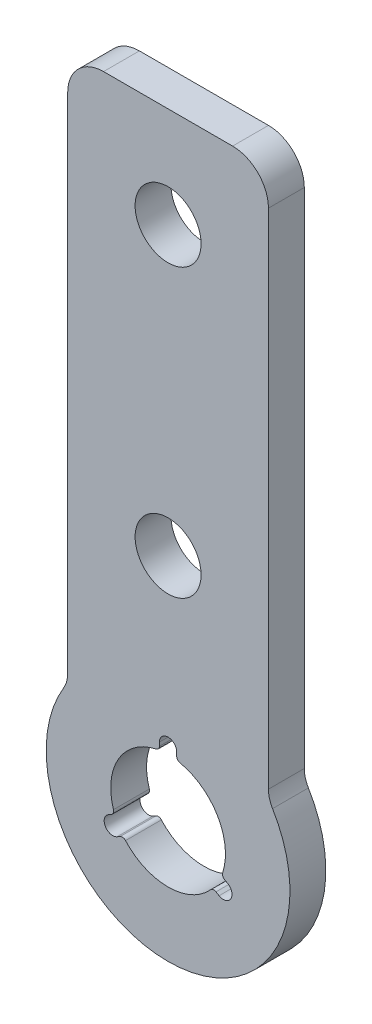
SolidWorks part; units mm, degrees
material "6061 合金"
ref_plane "前视基准面" through (0, 0, 0) normal (0, 0, 1) x (1, 0, 0)
ref_plane "上视基准面" through (0, 0, 0) normal (0, 1, 0) x (1, 0, 0)
ref_plane "右视基准面" through (0, 0, 0) normal (1, 0, 0) x (0, 0, -1)
sketch "草图1" plane through (0, 0, 0) normal (0, 0, 1) x (1, 0, 0)
  line L0 (7.1834, -12.4844) -> (7.1834, 22.6072)
  line L1 (4.6834, 25.1072) -> (-4.3166, 25.1072)
  line L2 (-6.8166, 22.6072) -> (-6.8166, -12.4844)
  line L3 (4.3413, -19.6005) -> (4.1248, -19.4755)
  line L4 (3.5248, -20.5147) -> (3.7413, -20.6397)
  line L5 (-3.3746, -20.6397) -> (-3.1581, -20.5147)
  line L6 (-3.7581, -19.4755) -> (-3.9746, -19.6005)
  line L7 (-0.4166, -13.438) -> (-0.4166, -13.688)
  line L8 (0.7834, -13.688) -> (0.7834, -13.438)
  arc A0 (2.4834, -1.8928) -> (-2.1166, -1.8928) centre (0.1834, -1.8928) ccw
  arc A1 (-7.1024, -13.5146) -> (-6.8166, -12.4844) centre (-8.8166, -12.4844) ccw
  arc A2 (-7.1024, -13.5146) -> (7.4691, -13.5146) centre (0.1834, -17.8928) ccw
  arc A3 (7.1834, -12.4844) -> (7.4691, -13.5146) centre (9.1834, -12.4844) ccw
  arc A4 (7.1834, 22.6072) -> (4.6834, 25.1072) centre (4.6834, 22.6072) ccw
  arc A5 (-4.3166, 25.1072) -> (-6.8166, 22.6072) centre (-4.3166, 22.6072) ccw
  arc A6 (-2.1166, -1.8928) -> (2.4834, -1.8928) centre (0.1834, -1.8928) ccw
  arc A7 (2.4834, 18.1072) -> (-2.1166, 18.1072) centre (0.1834, 18.1072) ccw
  arc A8 (-2.1166, 18.1072) -> (2.4834, 18.1072) centre (0.1834, 18.1072) ccw
  arc A9 (3.9893, -19.1234) -> (1.0206, -13.9813) centre (0.1834, -17.8928) ccw
  arc A10 (3.9893, -19.1234) -> (4.1248, -19.4755) centre (4.2748, -19.2157) ccw
  arc A11 (3.7413, -20.6397) -> (4.3413, -19.6005) centre (4.0413, -20.1201) ccw
  arc A12 (3.5248, -20.5147) -> (3.1521, -20.5735) centre (3.3748, -20.7746) ccw
  arc A13 (-2.7854, -20.5735) -> (3.1521, -20.5735) centre (0.1834, -17.8928) ccw
  arc A14 (-2.7854, -20.5735) -> (-3.1581, -20.5147) centre (-3.0081, -20.7746) ccw
  arc A15 (-3.9746, -19.6005) -> (-3.3746, -20.6397) centre (-3.6746, -20.1201) ccw
  arc A16 (-3.7581, -19.4755) -> (-3.6226, -19.1234) centre (-3.9081, -19.2157) ccw
  arc A17 (-0.6539, -13.9813) -> (-3.6226, -19.1234) centre (0.1834, -17.8928) ccw
  arc A18 (-0.6539, -13.9813) -> (-0.4166, -13.688) centre (-0.7166, -13.688) ccw
  arc A19 (0.7834, -13.438) -> (-0.4166, -13.438) centre (0.1834, -13.438) ccw
  arc A20 (0.7834, -13.688) -> (1.0206, -13.9813) centre (1.0834, -13.688) ccw
extrude "凸台-拉伸1" add sketch "草图1" along normal blind 2.5
